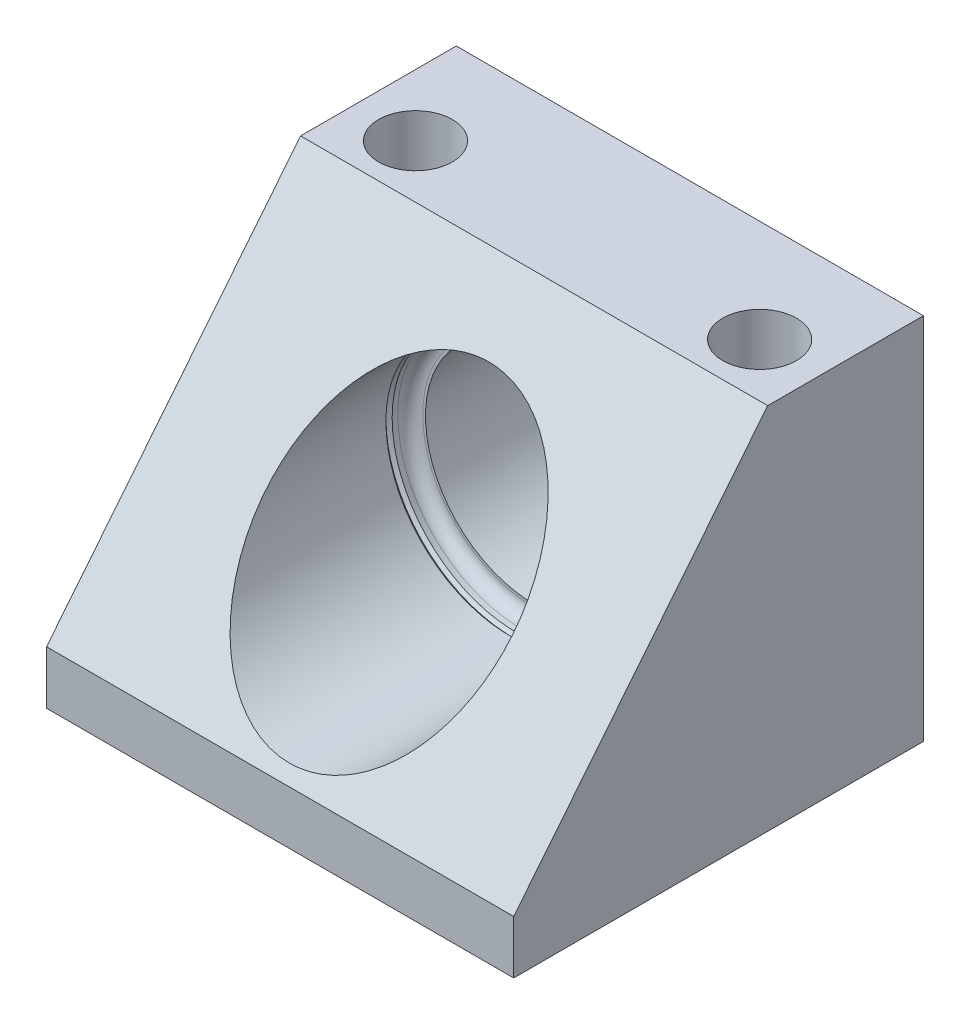
SolidWorks part; units mm, degrees
material "Alloy Steel"
ref_plane "Front Plane" through (0, 0, 0) normal (0, 0, 1) x (1, 0, 0)
ref_plane "Top Plane" through (0, 0, 0) normal (0, 1, 0) x (1, 0, 0)
ref_plane "Right Plane" through (0, 0, 0) normal (1, 0, 0) x (0, 0, -1)
sketch "Sketch1" plane through (0, 0, 0) normal (0, 0, 1) x (1, 0, 0)
  line L0 (28.4988, 0) -> (28.4988, 44.9834) construction
  line L1 (0, 44.9834) -> (56.9976, 44.9834)
  line L2 (0, 44.9834) -> (0, 0)
  line L3 (0, 0) -> (56.9976, 0)
  line L4 (56.9976, 44.9834) -> (56.9976, 0)
  circle A0 centre (28.4988, 23.0124) radius 13.259
  dimension "D4" = 26.518
  dimension "D1" = 56.9976
  dimension "D2" = 44.9834
  dimension "D3" = 23.0124
extrude "Extrude1" add sketch "Sketch1" against normal blind 49.9872
sketch "Sketch2" plane through (56.9976, 0, 0) normal (1, 0, 0) x (0, 0, -1)
  line L0 (0, 44.9834) -> (30.988, 44.9834)
  line L3 (49.9872, 44.9834) -> (0, 44.9834) construction
  line L4 (30.988, 44.9834) -> (0, 6.5024)
  line L5 (0, 0) -> (0, 44.9834) construction
  line L6 (0, 6.5024) -> (0, 44.9834)
  line L7 (49.9872, 0) -> (49.9872, 44.9834) construction
  line L8 (49.9872, 0) -> (0, 0) construction
  dimension "D2" = 6.5024
  dimension "D1" = 18.9992
extrude "Cut-Extrude1" cut sketch "Sketch2" against normal through all
sketch "Sketch3" plane through (0, 0, 0) normal (0, 0, -1) x (-1, 0, 0)
  circle A0 centre (-28.4988, 23.0124) radius 15.113
  dimension "D1" = 30.226
extrude "Cut-Extrude2" cut sketch "Sketch3" along normal offset from surface (30.988 mm away) 18.9992 up to face at (41.7578, 23.0124, -49.9872)
fillet "Fillet1" radius 1.524 1 edges at (43.6118, 23.0124, -30.988)
hole_wizard "Hole1" positions "Sketch5" profile "Sketch4" legacy end condition up to next
sketch "Sketch5" plane through (0, 44.9834, 0) normal (0, 1, 0) x (-1, 0, 0)
  line L0 (-56.9976, -49.9872) -> (-56.9976, -30.988) construction
  line L2 (-56.9976, -49.9872) -> (0, -49.9872) construction
  point P0 (-7.5184, -37.4904)
  point P1 (-49.5046, -37.4904)
  dimension "D1" = 7.493
  dimension "D2" = 12.4968
  dimension "D3" = 41.9862
sketch "Sketch4" plane through (7.5184, 44.9834, -37.4904) normal (1, 0, 0) x (0, 0, 1)
  line L0 (0, 0) -> (0, 44.9834)
  line L1 (0, 44.9834) -> (4.4958, 44.9834)
  line L2 (4.4958, 44.9834) -> (4.4958, 0)
  line L3 (4.4958, 0) -> (0, 0)
  line L4 (0, 110) -> (0, -10) construction
  dimension "Diameter" = 8.9916
  dimension "Depth" = 44.9834
ref_plane "Plane1" through (0, 23.0124, 0) normal (0, 1, 0) x (-1, 0, 0)
sketch "Sketch6" plane through (0, 23.0124, 0) normal (0, 1, 0) x (-1, 0, 0)
  line L0 (-13.3858, -28.0162) -> (-13.3858, -28.7782)
  line L1 (-13.3858, -29.464) -> (-13.3858, -13.2952) construction
  line L2 (-13.3858, -28.7782) -> (-13.0048, -28.3972)
  line L3 (-13.0048, -28.3972) -> (-13.3858, -28.0162)
  line L4 (-28.4988, 17.5081) -> (-28.4988, -67.5449) construction
  line L5 (-28.4988, -49.9872) -> (-28.4988, -30.988) construction
  line L6 (-56.9976, -49.9872) -> (0, -49.9872) construction
  line L7 (-15.2398, -48.8952) -> (-15.2398, -49.9872)
  line L8 (-15.2398, -49.9872) -> (-15.2398, -30.988) construction
  line L9 (-15.2398, -49.9872) -> (-14.1478, -49.9872)
  line L10 (-14.1478, -49.9872) -> (-15.2398, -48.8952)
  dimension "D1" = 90
  dimension "D2" = 45
  dimension "D3" = 0.762
  dimension "D4" = 21.59
  dimension "D5" = 45
  dimension "D6" = 28.702
revolve "Cut-Revolve1" cut sketch "Sketch6" angle 360 about L4
